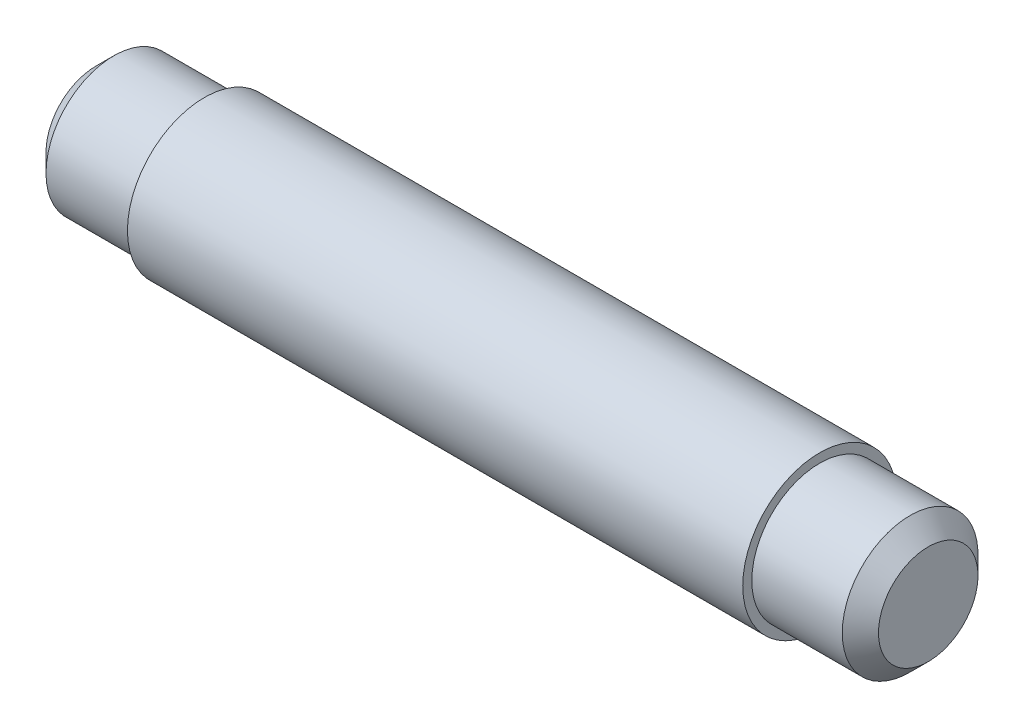
SolidWorks part; units mm, degrees
ref_plane "Płaszczyzna przednia" through (0, 0, 0) normal (0, 0, 1) x (1, 0, 0)
ref_plane "Płaszczyzna górna" through (0, 0, 0) normal (0, 1, 0) x (1, 0, 0)
ref_plane "Płaszczyzna prawa" through (0, 0, 0) normal (1, 0, 0) x (0, 0, -1)
sketch "Szkic1" plane through (0, 0, 0) normal (0, 0, 1) x (1, 0, 0)
  line L0 (0, 0) -> (46, 0)
  line L1 (46, 0) -> (46, 2.75)
  line L2 (45, 3.75) -> (40, 3.75)
  line L3 (40, 3.75) -> (40, 4.25)
  line L4 (40, 4.25) -> (6, 4.25)
  line L5 (6, 4.25) -> (6, 3.75)
  line L6 (6, 3.75) -> (1, 3.75)
  line L7 (0, 2.75) -> (0, 0)
  line L8 (1, 3.75) -> (0, 2.75)
  line L9 (46, 2.75) -> (45, 3.75)
  point P3 (44.7893, 0)
  point P4 (46, 3.75)
  point P9 (0, 3.75)
  point P10 (47.0569, 0)
  dimension "D1" = 6
  dimension "D2" = 34
  dimension "D3" = 3.75
  dimension "D4" = 4.25
  dimension "D5" = 6
revolve "Obrót1" add sketch "Szkic1" angle 360 about L0
